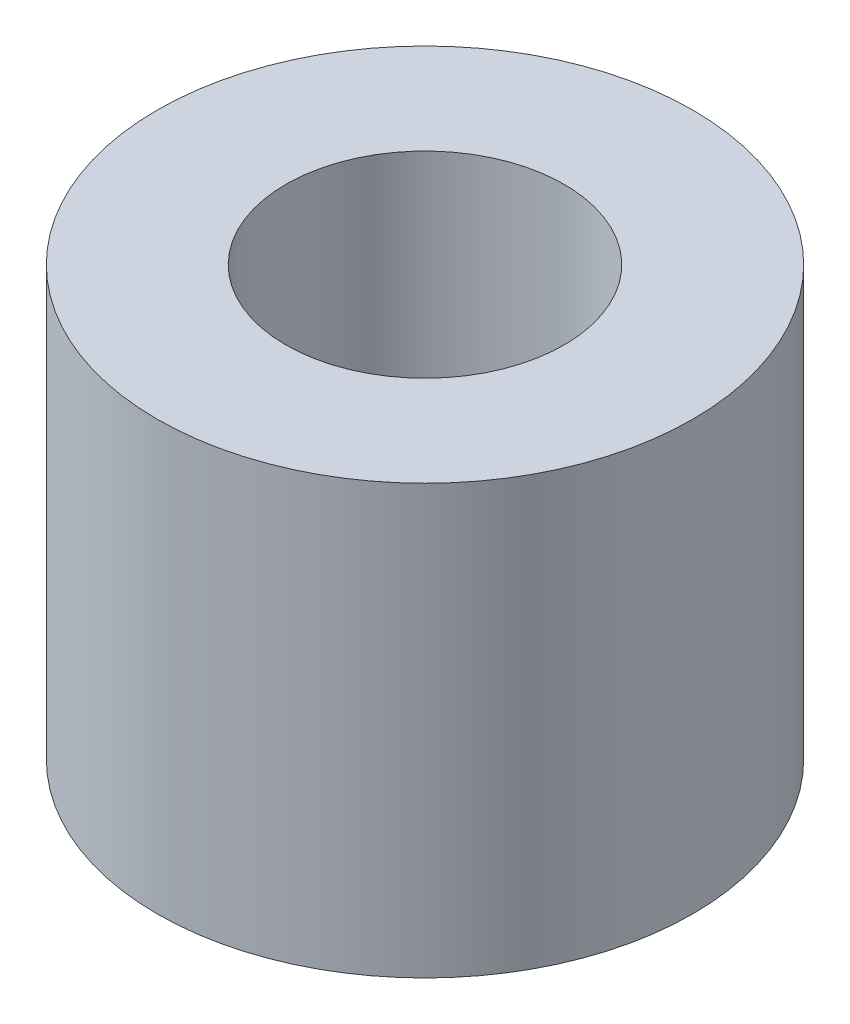
SolidWorks part; units mm, degrees
ref_plane "Front Plane" through (0, 0, 0) normal (0, 0, 1) x (1, 0, 0)
ref_plane "Top Plane" through (0, 0, 0) normal (0, 1, 0) x (1, 0, 0)
ref_plane "Right Plane" through (0, 0, 0) normal (1, 0, 0) x (0, 0, -1)
sketch "Sketch1" plane through (0, 0, 0) normal (0, 1, 0) x (1, 0, 0)
  circle A0 centre (0, 0) radius 3.175
  dimension "D1" = 6.35
extrude "Boss-Extrude1" add sketch "Sketch1" along normal mid plane 5.08
hole_wizard "M4x0.7 Tapped Hole1" positions "Sketch3" profile "Sketch2" tap size "M4x0.7" standard "ANSI Metric"
sketch "Sketch3" plane through (0, 2.54, 0) normal (0, 1, 0) x (1, 0, 0)
  point P0 (0, 0)
sketch "Sketch2" plane through (0, 2.54, 0) normal (1, 0, 0) x (0, 0, 1)
  line L0 (0, 0) -> (0, 9.906)
  line L1 (0, 9.906) -> (1.65, 9.906)
  line L2 (1.65, 9.906) -> (1.65, 0)
  line L5 (1.65, 0) -> (0, 0)
  line L10 (0, 9.906) -> (-1.65, 9.906) construction
  line L11 (0, -6.35) -> (0, 107.95) construction
  dimension "Tap Drill Dia." = 3.3
  dimension "Tap Drill Depth" = 9.906
  dimension "Drill Angle" = 180
cosmetic thread "Hole Thread1" parameters "D1"=5.08, "D2"=4
